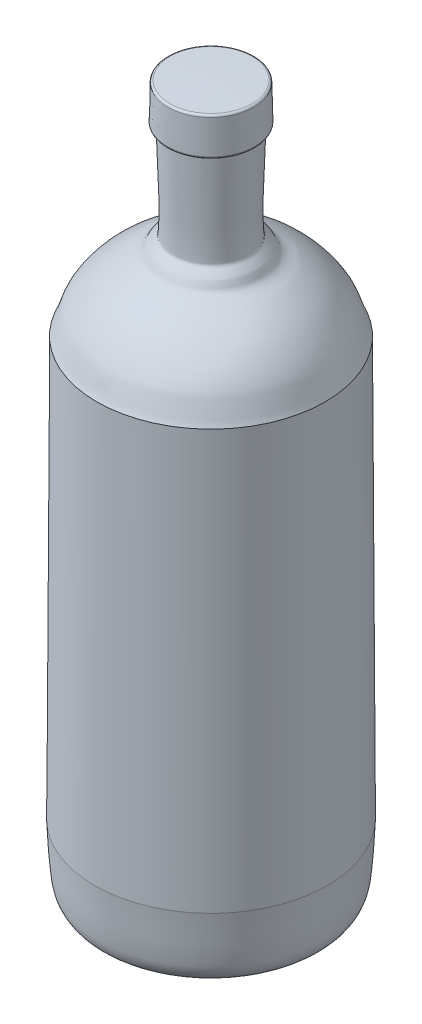
SolidWorks part; units mm, degrees
other "Kamera1"
ref_plane "Ebene vorne" through (0, 0, 0) normal (0, 0, 1) x (1, 0, 0)
ref_plane "Ebene oben" through (0, 0, 0) normal (0, 1, 0) x (1, 0, 0)
ref_plane "Ebene rechts" through (0, 0, 0) normal (1, 0, 0) x (0, 0, -1)
sketch "Skizze1" plane through (0, 0, 0) normal (0, 0, 1) x (1, 0, 0)
  line L0 (118.802, 1022.1967) -> (176.9645, 1024.1037)
  line L1 (176.9645, 1024.1037) -> (177, 1023.8881)
  line L2 (177, 0.3486) -> (177, 1023.8881)
  line L8 (12, 115) -> (14.9987, 707.7419)
  line L9 (119.8375, 967.7581) -> (116.8684, 968.7719)
  line L10 (114.8386, 971.678) -> (115.9011, 1019.2653)
  line L11 (177, 1120.9718) -> (177, -171.7317) construction
  arc A0 (118.802, 1022.1967) -> (115.9011, 1019.2653) centre (118.9004, 1019.1983) ccw
  arc A1 (121.8676, 964.9734) -> (119.8375, 967.7581) centre (118.8681, 964.9191) ccw
  arc A2 (116.8684, 968.7719) -> (114.8386, 971.678) centre (117.8379, 971.611) cw
  spline S1 degree 3 poles (177, 0.3486) (155.8659, -0.0496) (134.7869, 0.6374) (114, 4) (102.4836, 5.8629) (64.1531, 4.6091) (44, 16) (37.6291, 19.601) (29.8956, 21.5604) (25, 27) (20.403, 32.1078) (18.0043, 39.2019) (17, 46) (13.6299, 68.8127) (13.6667, 92) (12, 115) knots 3.482219 3.482219 3.482219 3.482219 4 4 4 5 5 5 6 6 6 7 7 7 8 8 8 8
  spline S2 degree 3 poles (14.9987, 707.7419) (20.9814, 719.4933) (22.7351, 733.1839) (29.2667, 744.6393) (35.7397, 755.9918) (44.1836, 766.2911) (53.491, 775.4644) (62.4654, 784.3096) (73.1529, 791.2863) (83.6571, 798.2462) (90.6205, 802.8601) (99.2697, 804.8073) (105.7435, 810.0863) (109.3324, 813.0128) (110.0251, 818.3508) (112.8304, 822.0352) (116.1176, 826.3525) (123.5748, 828.5396) (123.9172, 833.9551) (126.6732, 877.5461) (122.5508, 921.3006) (121.8676, 964.9734) knots 0 0 0 0 1 1 1 2 2 2 3 3 3 4 4 4 5 5 5 6 6 6 7 7 7 7
  dimension "D1" = 3
  dimension "D2" = 3
revolve "Rotation1" add sketch "Skizze1" angle 360 about L11
